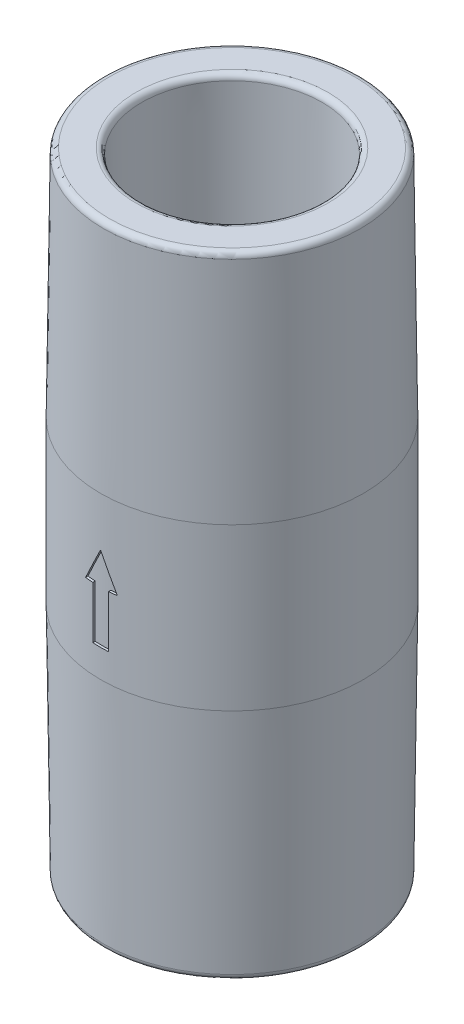
SolidWorks part; units mm, degrees
ref_plane "Front Plane" through (0, 0, 0) normal (0, 0, 1) x (1, 0, 0)
ref_plane "Top Plane" through (0, 0, 0) normal (0, 1, 0) x (1, 0, 0)
ref_plane "Right Plane" through (0, 0, 0) normal (1, 0, 0) x (0, 0, -1)
ref_plane "Plane2" through (0, 16.7519, 0) normal (0, 1, 0) x (1, 0, 0)
sketch "Sketch2" plane through (0, 16.7519, 0) normal (0, 1, 0) x (1, 0, 0)
  line L24 (4.062, -0.75) -> (7.3951, -0.75)
  line L25 (7.3951, 0.75) -> (4.062, 0.75)
  line L26 (2.6805, 3.1428) -> (4.3471, 6.0293)
  line L27 (3.048, 6.7793) -> (1.3815, 3.8928)
  line L28 (-1.3815, 3.8928) -> (-3.048, 6.7793)
  line L29 (-4.3471, 6.0293) -> (-2.6805, 3.1428)
  line L30 (-4.062, 0.75) -> (-7.3951, 0.75)
  line L31 (-7.3951, -0.75) -> (-4.062, -0.75)
  line L32 (-2.6805, -3.1428) -> (-4.3471, -6.0293)
  line L33 (-3.048, -6.7793) -> (-1.3815, -3.8928)
  line L34 (1.3815, -3.8928) -> (3.048, -6.7793)
  line L35 (4.3471, -6.0293) -> (2.6805, -3.1428)
  arc A72 (7.8881, -1.3333) -> (7.3951, -0.75) centre (7.3951, -1.25) ccw
  arc A73 (7.8881, -1.3333) -> (7.8881, 1.3333) centre (0, 0) ccw
  arc A74 (7.3951, 0.75) -> (7.8881, 1.3333) centre (7.3951, 1.25) ccw
  arc A75 (3.5841, 1.1029) -> (4.062, 0.75) centre (4.062, 1.25) ccw
  arc A76 (3.5841, 1.1029) -> (2.7472, 2.5525) centre (0, 0) ccw
  arc A77 (2.6805, 3.1428) -> (2.7472, 2.5525) centre (3.1135, 2.8928) ccw
  arc A78 (5.0988, 6.1646) -> (4.3471, 6.0293) centre (4.7801, 5.7793) ccw
  arc A79 (5.0988, 6.1646) -> (2.7894, 7.498) centre (0, 0) ccw
  arc A80 (3.048, 6.7793) -> (2.7894, 7.498) centre (2.615, 7.0293) ccw
  arc A81 (0.8369, 3.6554) -> (1.3815, 3.8928) centre (0.9485, 4.1428) ccw
  arc A82 (0.8369, 3.6554) -> (-0.8369, 3.6554) centre (0, 0) ccw
  arc A83 (-1.3815, 3.8928) -> (-0.8369, 3.6554) centre (-0.9485, 4.1428) ccw
  arc A84 (-2.7894, 7.498) -> (-3.048, 6.7793) centre (-2.615, 7.0293) ccw
  arc A85 (-2.7894, 7.498) -> (-5.0988, 6.1646) centre (0, 0) ccw
  arc A86 (-4.3471, 6.0293) -> (-5.0988, 6.1646) centre (-4.7801, 5.7793) ccw
  arc A87 (-2.7472, 2.5525) -> (-2.6805, 3.1428) centre (-3.1135, 2.8928) ccw
  arc A88 (-2.7472, 2.5525) -> (-3.5841, 1.1029) centre (0, 0) ccw
  arc A89 (-4.062, 0.75) -> (-3.5841, 1.1029) centre (-4.062, 1.25) ccw
  arc A90 (-7.8881, 1.3333) -> (-7.3951, 0.75) centre (-7.3951, 1.25) ccw
  arc A91 (-7.8881, 1.3333) -> (-7.8881, -1.3333) centre (0, 0) ccw
  arc A92 (-7.3951, -0.75) -> (-7.8881, -1.3333) centre (-7.3951, -1.25) ccw
  arc A93 (-3.5841, -1.1029) -> (-4.062, -0.75) centre (-4.062, -1.25) ccw
  arc A94 (-3.5841, -1.1029) -> (-2.7472, -2.5525) centre (0, 0) ccw
  arc A95 (-2.6805, -3.1428) -> (-2.7472, -2.5525) centre (-3.1135, -2.8928) ccw
  arc A96 (-5.0988, -6.1646) -> (-4.3471, -6.0293) centre (-4.7801, -5.7793) ccw
  arc A97 (-5.0988, -6.1646) -> (-2.7894, -7.498) centre (0, 0) ccw
  arc A98 (-3.048, -6.7793) -> (-2.7894, -7.498) centre (-2.615, -7.0293) ccw
  arc A99 (-0.8369, -3.6554) -> (-1.3815, -3.8928) centre (-0.9485, -4.1428) ccw
  arc A100 (-0.8369, -3.6554) -> (0.8369, -3.6554) centre (0, 0) ccw
  arc A101 (1.3815, -3.8928) -> (0.8369, -3.6554) centre (0.9485, -4.1428) ccw
  arc A102 (2.7894, -7.498) -> (3.048, -6.7793) centre (2.615, -7.0293) ccw
  arc A103 (2.7894, -7.498) -> (5.0988, -6.1646) centre (0, 0) ccw
  arc A104 (4.3471, -6.0293) -> (5.0988, -6.1646) centre (4.7801, -5.7793) ccw
  arc A105 (2.7472, -2.5525) -> (2.6805, -3.1428) centre (3.1135, -2.8928) ccw
  arc A106 (2.7472, -2.5525) -> (3.5841, -1.1029) centre (0, 0) ccw
  arc A107 (4.062, -0.75) -> (3.5841, -1.1029) centre (4.062, -1.25) ccw
sketch "Sketch1" plane through (0, 0, 0) normal (1, 0, 0) x (0, 0, -1)
  line L0 (0, 25.7767) -> (0, -25.7767) construction
  line L1 (7.725, 54) -> (7.55, 38.7719)
  line L3 (10, 32.8719) -> (10, 29.6119)
  line L4 (10, 29.6119) -> (8, 29.6119)
  line L5 (8, 29.6119) -> (8, 16.7519)
  line L6 (8, 16.7519) -> (7.41, 15.73)
  line L7 (7.41, 15.73) -> (7.725, 0)
  line L8 (7.725, 0) -> (11, 0)
  line L9 (11, 0) -> (11, 54) construction
  line L10 (11, 54) -> (7.725, 54)
  line L11 (7.55, 38.7719) -> (10, 32.8719)
  line L12 (11, 54) -> (11.25, 34)
  line L13 (11.25, 34) -> (11.25, 20.2)
  line L14 (11.25, 20.2) -> (11, 0)
  dimension "D1" = 54
  dimension "D3" = 10
  dimension "D4" = 11
  dimension "D8" = 2
  dimension "D9" = 7.725
  dimension "D2" = 7.725
  dimension "D12" = 5.9
  dimension "D11" = 7.55
  dimension "D13" = 3.26
  dimension "D6" = 12.86
  dimension "D5" = 8
  dimension "D7" = 60
  dimension "D10" = 1.18
  dimension "D14" = 15.73
  dimension "D15" = 20
  dimension "D16" = 20.2
  dimension "D17" = 11.25
revolve "Revolve1" add sketch "Sketch1" angle 360 about L0
extrude "Boss-Extrude4" add sketch "Sketch2" along normal up to surface (12.86 mm away) up to face at (0, 29.6119, 8)
sketch "Sketch3" plane through (0, 0, 0) normal (0, 0, 1) x (1, 0, 0)
  line L0 (-8, 16.7519) -> (8, 16.7519) construction
  line L1 (-8, 16.7519) -> (-2.4213, 16.7519) construction
  line L4 (-2.6, 26.1119) -> (-8, 16.7519)
  line L5 (0, 0) -> (0, 27.6119) construction
  line L6 (0.8369, 29.6119) -> (-0.8369, 29.6119) construction
  line L9 (0, 27.6119) -> (0, 16.7519)
  line L12 (-8, 16.7519) -> (-7.8881, 16.7519) construction
  line L13 (-0.8369, 16.7519) -> (0.8369, 16.7519) construction
  line L14 (0, 16.7519) -> (-8, 16.7519)
  line L18 (-8, 16.7519) -> (-7.8881, 16.7519) construction
  arc A1 (-2.6, 26.1119) -> (0, 27.6119) centre (-0.0029, 24.6136) cw
  point P8 (-7.3951, 15.7699)
  point P10 (-6.4464, 15.73)
  point P15 (-7.3835, 15.7499)
  point P16 (-6.9702, 16.7519)
  point P19 (0, 0)
  point P21 (-8.0179, 16.7519)
  dimension "D1" = 2
  dimension "D2" = 1.5
  dimension "D3" = 2.6
revolve "Cut-Revolve1" cut sketch "Sketch3" angle 360 about L5
sketch "Sketch4" plane through (0, 0, 0) normal (0, 0, 1) x (1, 0, 0)
  line L0 (0, 0) -> (0, 64.2909) construction
  line L1 (-2.5, 29.6119) -> (-2.5, 31.1119)
  line L2 (10, 29.6119) -> (-10, 29.6119) construction
  line L3 (-2.5, 31.1119) -> (-3.25, 31.1119)
  line L4 (0, 34.3619) -> (0, 29.6119)
  line L5 (0, 29.6119) -> (-2.5, 29.6119)
  arc A0 (-3.25, 31.1119) -> (0, 34.3619) centre (0, 31.1119) cw
  dimension "D1" = 1.5
  dimension "D2" = 3.25
  dimension "D3" = 2.5
revolve "Revolve2" add sketch "Sketch4" angle 360 about L0
fillet "Fillet1" radius 1 1 edges at (0, 15.73, 7.41)
fillet "Fillet2" radius 0.25 3 edges at (0, 29.6119, 10) (0, 29.6119, -2.5) (0, 31.1119, -2.5)
fillet "Fillet3" radius 3 2 edges at (0, 32.8719, 10) (0, 38.7719, 7.55)
fillet "Fillet4" radius 0.5 4 edges at (0, 0, 7.725) (0, 54, 7.725) (0, 0, 11) (0, 54, 11)
sketch "Sketch7" plane through (0, 0, 0) normal (0, 0, 1) x (1, 0, 0)
  line L0 (0, 0) -> (0, 56.2625) construction
  line L1 (-10.5061, 0) -> (10.5061, 0) construction
  line L2 (0, 29.816) -> (1.3603, 27.0578)
  line L3 (1.3603, 27.0578) -> (0.6764, 27.0578)
  line L4 (0.6764, 27.0578) -> (0.6764, 22.5906)
  line L5 (0.6764, 22.5906) -> (-0.6764, 22.5906)
  line L6 (-0.6764, 27.0578) -> (-0.6764, 22.5906)
  line L7 (-1.3603, 27.0578) -> (-0.6764, 27.0578)
  line L8 (0, 29.816) -> (-1.3603, 27.0578)
  point P9 (0, 30.8888)
  point P10 (0.6764, 27.5729)
  point P11 (0, 29.816)
  point P12 (1.3603, 27.0578)
  point P14 (0, 22.5906)
extrude "Cut-Extrude7" cut sketch "Sketch7" against normal blind 0.2 from surface starting at face at (0, 34, 11.25)
mirror "Mirror1" about plane through (0, 0, 0) normal (0, 0, 1) of "Cut-Extrude7"
equation "\"D2@Sketch1\"=\"D9@Sketch1\""
